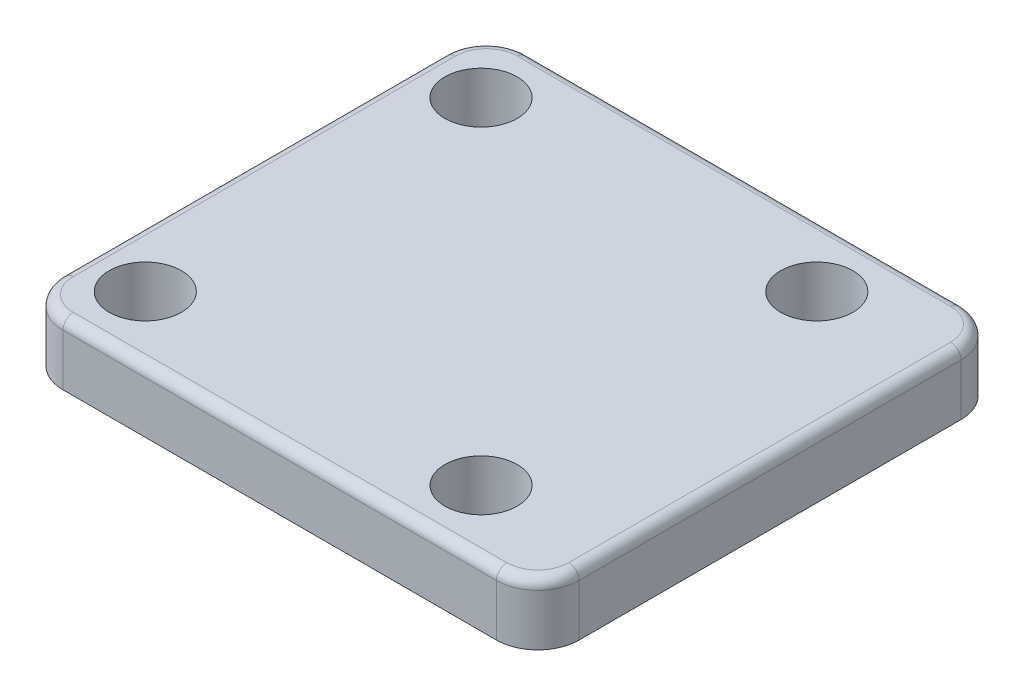
SolidWorks part; units mm, degrees
ref_plane "Front Plane" through (0, 0, 0) normal (0, 0, 1) x (1, 0, 0)
ref_plane "Top Plane" through (0, 0, 0) normal (0, 1, 0) x (1, 0, 0)
ref_plane "Right Plane" through (0, 0, 0) normal (1, 0, 0) x (0, 0, -1)
sketch "Sketch1" plane through (0, 0, 0) normal (0, 1, 0) x (1, 0, 0)
  line L1 (-18, 22.5) -> (24, 22.5)
  line L2 (-22, 18.5) -> (-22, -18.5)
  line L3 (-18, -22.5) -> (24, -22.5)
  line L4 (28, 18.5) -> (28, -18.5)
  arc A0 (24, 22.5) -> (28, 18.5) centre (24, 18.5) cw
  arc A1 (-22, -18.5) -> (-18, -22.5) centre (-18, -18.5) ccw
  arc A2 (24, -22.5) -> (28, -18.5) centre (24, -18.5) ccw
  arc A3 (-18, 22.5) -> (-22, 18.5) centre (-18, 18.5) ccw
  point P7 (28, 22.5)
  point P12 (28, -22.5)
  point P15 (-22, 22.5)
  dimension "D5" = 4
  dimension "D1" = 50
  dimension "D2" = 45
  dimension "D3" = 22
  dimension "D4" = 22.5
extrude "Boss-Extrude1" add sketch "Sketch1" along normal blind 6
fillet "Fillet1" radius 1 8 edges at (28, 6, 0) (26.8284, 6, 21.3284) (3, 6, 22.5) (-20.8284, 6, 21.3284) (-22, 6, 0) (-20.8284, 6, -21.3284) (3, 6, -22.5) (26.8284, 6, -21.3284)
sketch "Sketch2" plane through (0, 0, 0) normal (0, -1, 0) x (1, 0, 0)
  circle A0 centre (0, 0) radius 16
  dimension "D1" = 32
extrude "Boss-Extrude2" add sketch "Sketch2" along normal blind 2
chamfer "Chamfer1" distance 1 angle 60 1 edges at (0, -2, -16)
sketch "Sketch3" plane through (0, 6, 0) normal (0, 1, 0) x (1, 0, 0)
  line L0 (-16.2635, 16.2635) -> (0, 0) construction
  line L1 (0, 0) -> (-23, 0) construction
  circle A0 centre (0, 0) radius 23 construction
  circle A1 centre (-16.2635, 16.2635) radius 3.5
  circle A2 centre (16.2635, 16.2635) radius 3.5
  circle A3 centre (16.2635, -16.2635) radius 3.5
  circle A4 centre (-16.2635, -16.2635) radius 3.5
  dimension "D1" = 46
  dimension "D3" = 7
  dimension "D2" = 45
  dimension "D4" = 4
extrude "Cut-Extrude1" cut sketch "Sketch3" against normal through all
